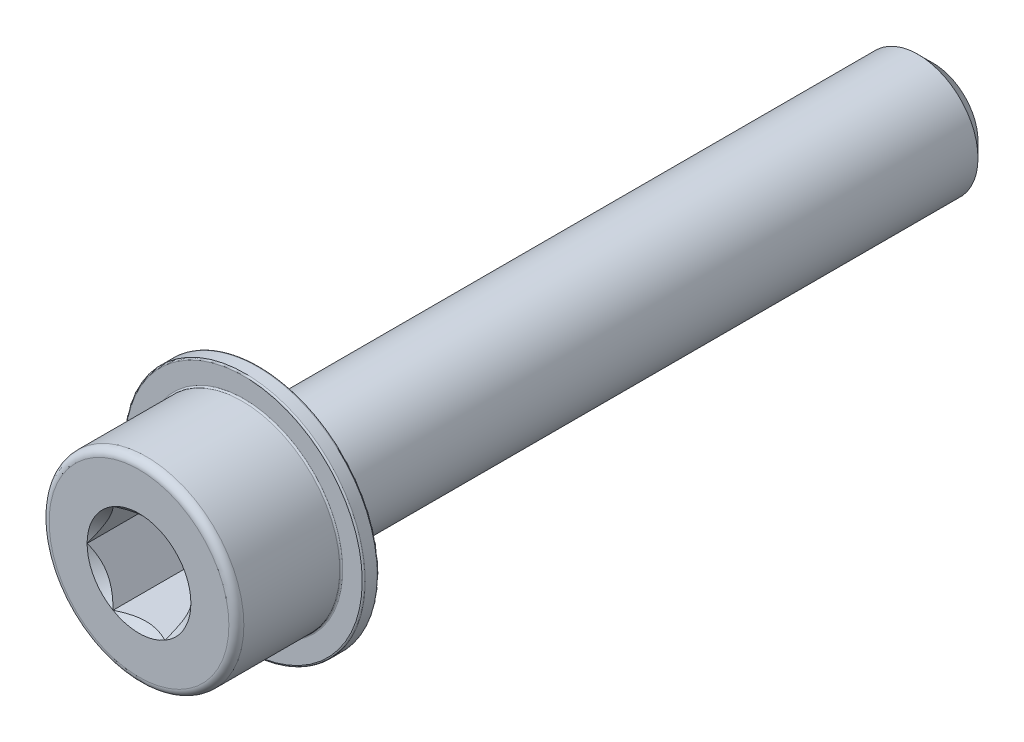
SolidWorks part; units mm, degrees
material "Acciaio inossidabile (ferroso)"
ref_plane "Piano frontale" through (0, 0, 0) normal (0, 0, 1) x (1, 0, 0)
ref_plane "Piano superiore" through (0, 0, 0) normal (0, 1, 0) x (1, 0, 0)
ref_plane "Piano destro" through (0, 0, 0) normal (1, 0, 0) x (0, 0, -1)
sketch "Schizzo1" plane through (0, 0, 0) normal (0, 0, 1) x (1, 0, 0)
  circle A0 centre (0, 0) radius 4
  dimension "D1" = 8
extrude "Estrusione-Estrusione1" add sketch "Schizzo1" along normal blind 45
cosmetic thread "Filettatura cosmetica2" parameters "D2"=6.619
chamfer "Smusso1" distance 1 angle 45 1 edges at (4, 0, 0)
sketch "Schizzo6" plane through (0, 0, 45) normal (0, 0, 1) x (1, 0, 0)
  circle A0 centre (0, 0) radius 6.5
  dimension "D1" = 13
extrude "Estrusione-Estrusione3" add sketch "Schizzo6" along normal blind 8
sketch "Schizzo7" plane through (0, 0, 53) normal (0, 0, 1) x (1, 0, 0)
  line L1 (1.7321, 3) -> (-1.7321, 3)
  line L2 (-1.7321, 3) -> (-3.4641, 0)
  line L3 (-3.4641, 0) -> (-1.7321, -3)
  line L4 (-1.7321, -3) -> (1.7321, -3)
  line L5 (1.7321, -3) -> (3.4641, 0)
  line L6 (3.4641, 0) -> (1.7321, 3)
  circle A1 centre (0, 0) radius 3 construction
  dimension "D1" = 6
extrude "Taglio-Estrusione3" cut sketch "Schizzo7" against normal blind 6
sketch "Schizzo8" plane through (0, 0, 53) normal (0, 0, 1) x (1, 0, 0)
  circle A0 centre (0, 0) radius 3.4641
extrude "Taglio-Estrusione4" cut sketch "Schizzo8" against normal blind 1 draft 45
fillet "Raccordo1" radius 0.5 1 edges at (6.5, 0, 53)
sketch "Schizzo9" plane through (0, 0, 45) normal (0, 0, -1) x (-1, 0, 0)
  circle A0 centre (0, 0) radius 6.5
  circle A1 centre (0, 0) radius 8
  dimension "D1" = 13
  dimension "D2" = 16
extrude "Estrusione-Estrusione4" add sketch "Schizzo9" against normal blind 1
fillet "Raccordo2" radius 0.1 3 edges at (-8, 0, 46) (-6.5, 0, 46) (-8, 0, 45)
